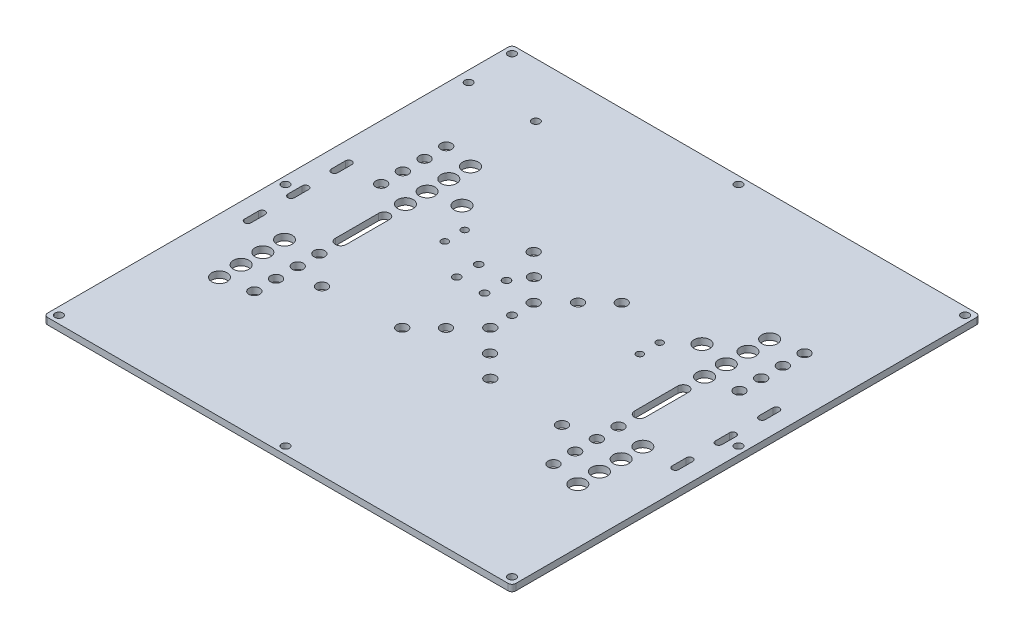
SolidWorks part; units mm, degrees
material "6061-T6 (SS)"
ref_plane "Front Plane" through (0, 0, 0) normal (0, 0, 1) x (1, 0, 0)
ref_plane "Top Plane" through (0, 0, 0) normal (0, 1, 0) x (1, 0, 0)
ref_plane "Right Plane" through (0, 0, 0) normal (1, 0, 0) x (0, 0, -1)
sketch "Sketch1" plane through (0, 0, 0) normal (0, 1, 0) x (1, 0, 0)
  line L0 (0, 0) -> (108, 0) construction
  line L1 (106.25, -108) -> (-106.25, -108)
  line L2 (108, -106.25) -> (108, 106.25)
  line L3 (106.25, 108) -> (-106.25, 108)
  line L4 (-108, -106.25) -> (-108, 106.25)
  line L5 (0, 0) -> (0, 108) construction
  line L6 (69, -10) -> (69, 10) construction
  line L7 (66.5, -10) -> (66.5, 10)
  line L8 (71.5, -10) -> (71.5, 10)
  line L9 (98.62, -3.25) -> (98.62, 3.25) construction
  line L10 (97.12, -3.25) -> (97.12, 3.25)
  line L11 (100.12, -3.25) -> (100.12, 3.25)
  line L12 (98.62, 16.75) -> (98.62, 23.25) construction
  line L13 (97.12, 16.75) -> (97.12, 23.25)
  line L14 (100.12, 16.75) -> (100.12, 23.25)
  line L15 (98.62, -16.75) -> (98.62, -23.25) construction
  line L16 (97.12, -16.75) -> (97.12, -23.25)
  line L17 (100.12, -16.75) -> (100.12, -23.25)
  line L18 (-98.62, -16.75) -> (-98.62, -23.25) construction
  line L19 (-97.12, -16.75) -> (-97.12, -23.25)
  line L20 (-100.12, -16.75) -> (-100.12, -23.25)
  line L21 (-98.62, -3.25) -> (-98.62, 3.25) construction
  line L22 (-97.12, -3.25) -> (-97.12, 3.25)
  line L23 (-100.12, -3.25) -> (-100.12, 3.25)
  line L24 (-98.62, 16.75) -> (-98.62, 23.25) construction
  line L25 (-97.12, 16.75) -> (-97.12, 23.25)
  line L26 (-100.12, 16.75) -> (-100.12, 23.25)
  line L27 (-69, -10) -> (-69, 10) construction
  line L28 (-66.5, -10) -> (-66.5, 10)
  line L29 (-71.5, -10) -> (-71.5, 10)
  line L30 (-82.65, -52.3) -> (-82.65, -42.3) construction
  line L31 (-82.65, 52.3) -> (-82.65, 42.3) construction
  line L32 (69, -49.85) -> (69, -39.85) construction
  arc A0 (-106.25, -108) -> (-108, -106.25) centre (-106.25, -106.25) cw
  arc A1 (106.25, -108) -> (108, -106.25) centre (106.25, -106.25) ccw
  arc A2 (108, 106.25) -> (106.25, 108) centre (106.25, 106.25) ccw
  arc A3 (-106.25, 108) -> (-108, 106.25) centre (-106.25, 106.25) ccw
  circle A4 centre (0, 104.5) radius 1.8
  circle A5 centre (-104.5, 104.5) radius 1.8
  circle A6 centre (104.5, 104.5) radius 1.8
  circle A7 centre (104.5, -104.5) radius 1.8
  circle A8 centre (0, -104.5) radius 1.8
  circle A9 centre (-104.5, -104.5) radius 1.8
  circle A10 centre (104.5, 0) radius 1.8
  circle A11 centre (-104.5, 0) radius 1.8
  circle A12 centre (0, 0) radius 1.8
  circle A13 centre (0, 10) radius 2.5
  circle A14 centre (-10.16, 20.32) radius 2.5
  circle A15 centre (-20.325, 30.32) radius 2.5
  circle A16 centre (20.325, 30.32) radius 2.5
  circle A17 centre (10.16, 20.32) radius 2.5
  circle A18 centre (-45, 23.12) radius 1.57
  circle A19 centre (-45, 14) radius 1.57
  circle A20 centre (-28, 12.64) radius 1.75
  circle A21 centre (-15.17, 12.64) radius 1.75
  circle A22 centre (-28, 2.5) radius 1.75
  circle A23 centre (-15.17, 2.5) radius 1.75
  circle A24 centre (20.325, -30.32) radius 2.5
  circle A25 centre (0, -10) radius 2.5
  circle A26 centre (10.16, -20.32) radius 2.5
  circle A27 centre (-10.16, -20.32) radius 2.5
  circle A28 centre (-20.325, -30.32) radius 2.5
  circle A29 centre (45, 14) radius 1.57
  circle A30 centre (45, 23.12) radius 1.57
  arc A31 (66.5, -10) -> (71.5, -10) centre (69, -10) ccw
  arc A32 (71.5, 10) -> (66.5, 10) centre (69, 10) ccw
  arc A33 (97.12, -3.25) -> (100.12, -3.25) centre (98.62, -3.25) ccw
  arc A34 (100.12, 3.25) -> (97.12, 3.25) centre (98.62, 3.25) ccw
  arc A35 (97.12, 16.75) -> (100.12, 16.75) centre (98.62, 16.75) ccw
  arc A36 (100.12, 23.25) -> (97.12, 23.25) centre (98.62, 23.25) ccw
  arc A37 (97.12, -16.75) -> (100.12, -16.75) centre (98.62, -16.75) cw
  arc A38 (100.12, -23.25) -> (97.12, -23.25) centre (98.62, -23.25) cw
  arc A39 (-97.12, -16.75) -> (-100.12, -16.75) centre (-98.62, -16.75) ccw
  arc A40 (-100.12, -23.25) -> (-97.12, -23.25) centre (-98.62, -23.25) ccw
  arc A41 (-97.12, -3.25) -> (-100.12, -3.25) centre (-98.62, -3.25) cw
  arc A42 (-100.12, 3.25) -> (-97.12, 3.25) centre (-98.62, 3.25) cw
  arc A43 (-97.12, 16.75) -> (-100.12, 16.75) centre (-98.62, 16.75) cw
  arc A44 (-100.12, 23.25) -> (-97.12, 23.25) centre (-98.62, 23.25) cw
  arc A45 (-66.5, -10) -> (-71.5, -10) centre (-69, -10) cw
  arc A46 (-71.5, 10) -> (-66.5, 10) centre (-69, 10) cw
  circle A47 centre (-82.65, -52.3) radius 3.6
  circle A48 centre (-82.65, -42.3) radius 3.6
  circle A49 centre (-82.65, -32.3) radius 3.6
  circle A50 centre (-82.65, -22.3) radius 3.6
  circle A51 centre (-82.65, 52.3) radius 2.5
  circle A52 centre (-82.65, 42.3) radius 2.5
  circle A53 centre (-82.65, 32.3) radius 2.5
  circle A54 centre (-82.65, 22.3) radius 2.5
  circle A55 centre (82.65, -42.3) radius 3.6
  circle A56 centre (82.65, -32.3) radius 3.6
  circle A57 centre (82.65, -22.3) radius 3.6
  circle A58 centre (82.65, 42.3) radius 2.5
  circle A59 centre (82.65, 32.3) radius 2.5
  circle A60 centre (82.65, 22.3) radius 2.5
  circle A61 centre (82.65, 52.3) radius 2.5
  circle A62 centre (82.65, -52.3) radius 3.6
  circle A63 centre (69, 49.85) radius 3.6
  circle A64 centre (69, -49.85) radius 2.5
  circle A65 centre (69, 39.85) radius 3.6
  circle A66 centre (69, 29.85) radius 3.6
  circle A67 centre (69, 19.85) radius 3.6
  circle A68 centre (69, -39.85) radius 2.5
  circle A69 centre (69, -29.85) radius 2.5
  circle A70 centre (69, -19.85) radius 2.5
  circle A71 centre (-69, 19.85) radius 3.6
  circle A72 centre (-69, 29.85) radius 3.6
  circle A73 centre (-69, 39.85) radius 3.6
  circle A74 centre (-69, -19.85) radius 2.5
  circle A75 centre (-69, -29.85) radius 2.5
  circle A76 centre (-69, -49.85) radius 2.5
  circle A77 centre (-69, 49.85) radius 3.6
  circle A78 centre (-69, -39.85) radius 2.5
  circle A79 centre (-55.35, 32.3) radius 3.6
  circle A80 centre (-55.35, -32.3) radius 2.5
  circle A81 centre (55.35, -32.3) radius 2.5
  circle A82 centre (55.35, 32.3) radius 3.6
  circle A83 centre (-103, 83) radius 1.8
  circle A84 centre (-72, 83) radius 1.8
  point P71 (69, 0)
  point P77 (98.62, 0)
  point P84 (98.62, 20)
  point P92 (98.62, -20)
  point P99 (-98.62, -20)
  point P106 (-98.62, 0)
  point P113 (-98.62, 20)
  point P120 (-69, 0)
  dimension "D2" = 1.75
  dimension "D3" = 3.6
  dimension "D5" = 3.5
  dimension "D7" = 5
  dimension "D10" = 20.32
  dimension "D19" = 3.5
  dimension "D6" = 3.6
  dimension "D14" = 3.14
  dimension "D22" = 15.17
  dimension "D30" = 7.2
  dimension "D50" = 25
  dimension "D1" = 216
  dimension "D4" = 3.5
  dimension "D8" = 10
  dimension "D9" = 216
  dimension "D11" = 40.65
  dimension "D12" = 20.32
  dimension "D13" = 30.32
  dimension "D15" = 9.12
  dimension "D16" = 45
  dimension "D17" = 14
  dimension "D18" = 2.5
  dimension "D20" = 10.14
  dimension "D21" = 12.83
  dimension "D24" = 5
  dimension "D25" = 69
  dimension "D26" = 6.5
  dimension "D27" = 3
  dimension "D28" = 20
  dimension "D29" = 29.62
  dimension "D31" = 82.65
  dimension "D23" = 20
  dimension "D32" = 55.7
  dimension "D34" = 10
  dimension "D35" = 55.7
  dimension "D37" = 10
  dimension "D38" = 58.15
  dimension "D39" = 99.7
  dimension "D41" = 10
  dimension "D43" = 10
  dimension "D44" = 69
  dimension "D45" = 45
  dimension "D46" = 55.35
  dimension "D47" = 64.6
  dimension "D48" = 5
  dimension "D49" = 31
  dimension "D33" = 4
  dimension "D36" = 4
  dimension "D40" = 4
  dimension "D42" = 4
extrude "Boss-Extrude1" add sketch "Sketch1" along normal blind 3
